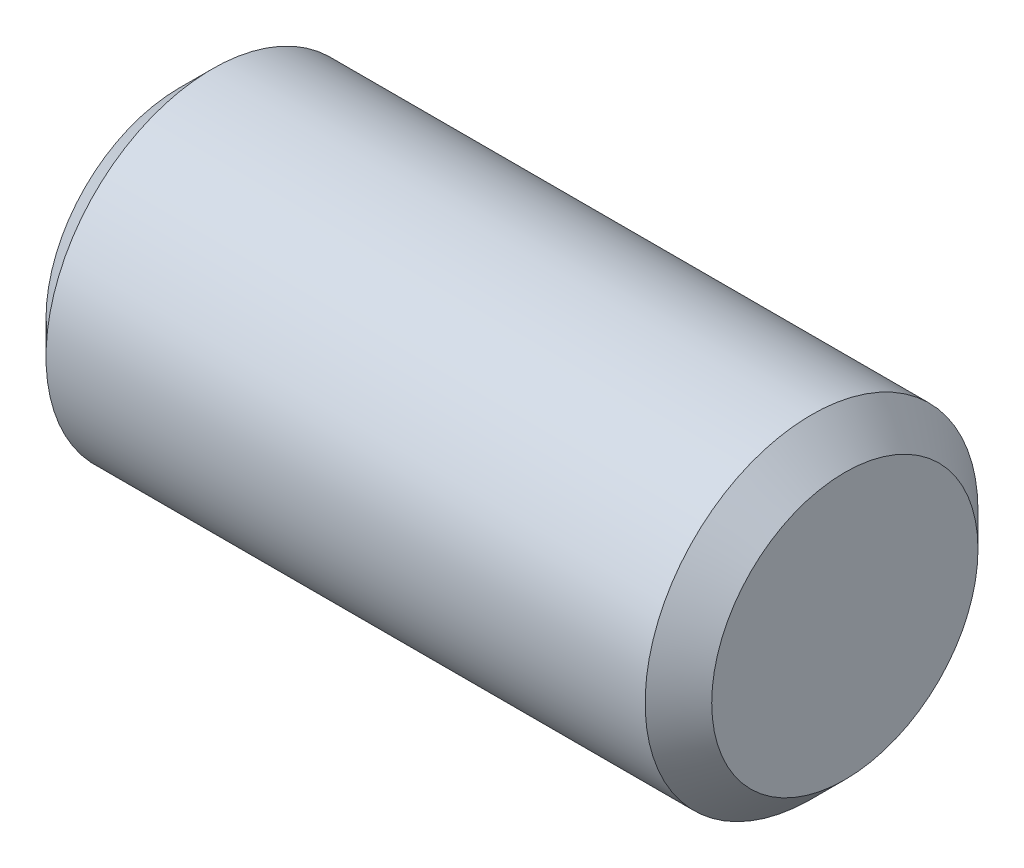
SolidWorks part; units mm, degrees
ref_plane "Front" through (0, 0, 0) normal (0, 0, 1) x (1, 0, 0)
ref_plane "Top" through (0, 0, 0) normal (0, 1, 0) x (1, 0, 0)
ref_plane "Right" through (0, 0, 0) normal (1, 0, 0) x (0, 0, -1)
sketch "Sketch1" plane through (0, 0, 0) normal (0, 0, 1) x (1, 0, 0)
  line L0 (-6.35, 0) -> (6.35, 0) construction
  line L1 (6.35, 3.175) -> (6.35, -3.175) construction
  line L2 (-6.35, 3.175) -> (-6.35, -3.175) construction
  dimension "Length" = 12.7
  dimension "Diameter" = 6.35
sketch "Sketch2" plane through (0, 0, 0) normal (1, 0, 0) x (0, 0, -1)
  circle A0 centre (0, 0) radius 3.175
extrude "Extrude1" add sketch "Sketch2" against normal up to vertex (6.35 mm away) and the other way up to vertex (6.35 mm away) up to point (-6.35, 3.175, 0) other way up to point (6.35, 3.175, 0)
chamfer "Chamfer1" distance 0.635 angle 45 2 edges at (6.35, 0, -3.175) (-6.35, 0, -3.175)
equation "\"D1@Chamfer1\" = \"Diameter@Sketch1\"*.1"
